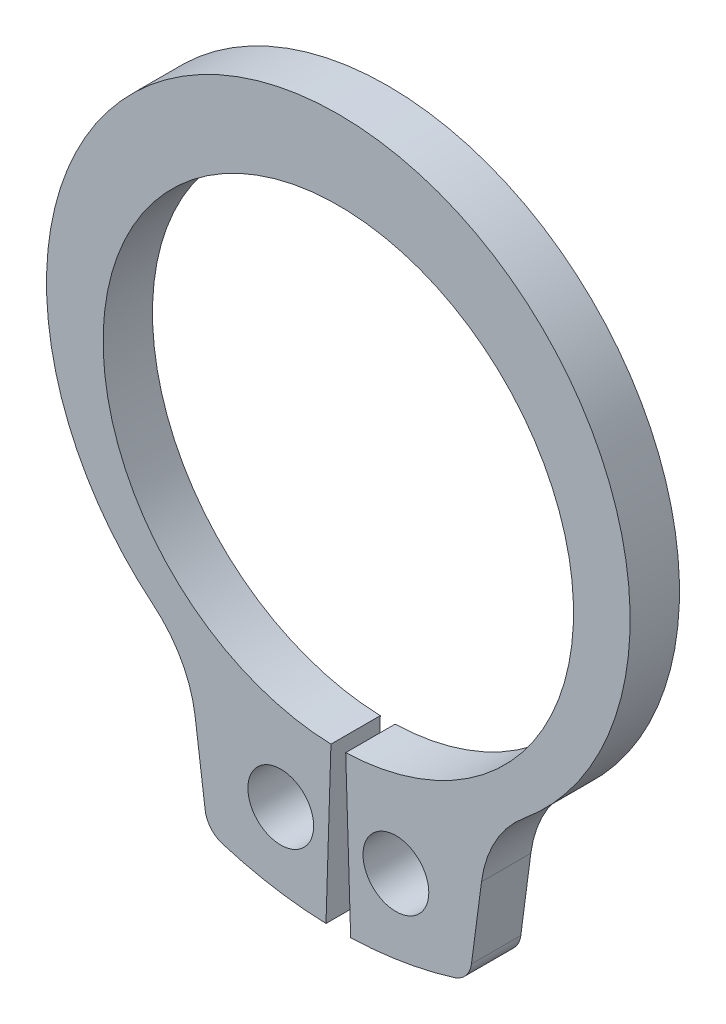
SolidWorks part; units mm, degrees
ref_plane "Plane1" through (0, 0, 0) normal (0, 0, 1) x (1, 0, 0)
ref_plane "Plane2" through (0, 0, 0) normal (0, 1, 0) x (1, 0, 0)
ref_plane "Plane3" through (0, 0, 0) normal (1, 0, 0) x (0, 0, -1)
sketch "Clipboard" plane through (0, 0, 0) normal (0, 0, 1) x (1, 0, 0)
  line L0 (0, 0) -> (2.4, 0)
  line L1 (0, 0) -> (0, 1.2)
  line L2 (0, 0) -> (0, -4.8)
  circle A0 centre (0, 0) radius 1
  circle A1 centre (0, 0) radius 7.5
  dimension "HoleDia" = 2
  dimension "ShaftDia" = 15
  dimension "LargeSection" = 2.4
  dimension "SmallSection" = 1.2
  dimension "LugSection" = 4.8
sketch "BodySke" plane through (0, 0, 0) normal (0, 0, 1) x (1, 0, 0)
  line L0 (-1.5431, 0) -> (1.5431, 0) construction
  line L1 (0, 0) -> (0, 9.55) construction
  line L2 (0.2244, -7.1465) -> (0.375, -11.9441)
  line L3 (-0.2244, -7.1465) -> (-0.375, -11.9441)
  line L4 (0, 0) -> (7.918, -8.9503) construction
  line L5 (0, 0) -> (-7.918, -8.9503) construction
  line L7 (4.3521, -8.4808) -> (4.0468, -10.7997)
  line L8 (-4.3521, -8.4808) -> (-4.0468, -10.7997)
  circle A0 centre (0, 0) radius 7.15 construction
  arc A1 (0.2244, -7.1465) -> (-0.2244, -7.1465) centre (0, 0) ccw
  arc A2 (5.5327, -6.254) -> (-5.5327, -6.254) centre (0, 0.6796) ccw construction
  arc A3 (0.375, -11.9441) -> (3.5244, -11.4185) centre (0, 0) ccw
  arc A4 (5.6337, -6.1721) -> (4.3521, -8.4808) centre (7.918, -8.9503) ccw
  arc A5 (-4.3521, -8.4808) -> (-5.6337, -6.1721) centre (-7.918, -8.9503) ccw
  arc A6 (-3.5244, -11.4185) -> (-0.375, -11.9441) centre (0, 0) ccw
  arc A7 (5.6337, -6.1721) -> (-5.6337, -6.1721) centre (0, 0.6796) ccw
  arc A8 (-4.3216, -8.712) -> (4.3216, -8.712) centre (0, 0) ccw construction
  circle A9 centre (1.75, -9.5662) radius 1
  circle A10 centre (-1.75, -9.5662) radius 1
  arc A11 (4.0468, -10.7997) -> (3.5244, -11.4185) centre (3.3032, -10.7018) cw
  arc A12 (-4.0468, -10.7997) -> (-3.5244, -11.4185) centre (-3.3032, -10.7018) ccw
  point P28 (3.9854, -11.2658)
  point P31 (-3.9854, -11.2658)
  dimension "HoleDia" = 2
  dimension "GrooveDia" = 14.3
  dimension "LugRad" = 11.95
  dimension "HoleOffsetRad" = 9.725
  dimension "D3" = 0.75
  dimension "LargeRad" = 9.55
  dimension "SmallRad" = 8.35
  dimension "SmallAngle" = 82.996
  dimension "D2" = 15
  dimension "HoleSpacing" = 3.5
  dimension "Gap" = 0.75
extrude "Body" add sketch "BodySke" against normal blind 1.5
sketch "NotSke" plane through (0, 0, 0) normal (0, 0, 1) x (1, 0, 0)
  line L0 (1.75, -8.5662) -> (1.75, -10.5662)
  line L1 (1.75, -10.5662) -> (-1.75, -10.5662)
  line L2 (-1.75, -10.5662) -> (-1.75, -8.5662)
  line L3 (-1.75, -8.5662) -> (1.75, -8.5662)
  circle A0 centre (1.75, -9.5662) radius 1 construction
  circle A1 centre (-1.75, -9.5662) radius 1 construction
extrude "Notch" [suppressed] cut sketch "NotSke" against normal through all
sketch "UnlSke" plane through (0, 0, 0) normal (0, 0, 1) x (1, 0, 0)
  line L0 (-3.3477, -11.4715) -> (-2.003, -6.8637)
  line L1 (3.3477, -11.4715) -> (2.003, -6.8637)
  arc A0 (2.003, -6.8637) -> (-2.003, -6.8637) centre (0, 0) ccw
  arc A1 (3.3477, -11.4715) -> (-3.3477, -11.4715) centre (0, 0) ccw
  arc A2 (0.375, -11.9441) -> (3.5244, -11.4185) centre (0, 0) ccw construction
  arc A3 (0.2244, -7.1465) -> (-0.2244, -7.1465) centre (0, 0) ccw construction
  circle A4 centre (-1.75, -9.5662) radius 1 construction
  circle A5 centre (1.75, -9.5662) radius 1 construction
extrude "Unlug" [suppressed] add sketch "UnlSke" against normal through all
equation "' \"ShaftDia@Clipboard\" = 15"
equation "' \"Thickness@Body\" = 1.5"
equation "' \"GrooveDia@BodySke\" = 14.3"
equation "' \"LugSection@Clipboard\" = 4.8"
equation "' \"LargeSection@Clipboard\" = 2.4"
equation "' \"HoleDia@Clipboard\" = 2.0"
equation "' \"ShaftDia@Clipboard\" = 50"
equation "' \"Thickness@Body\" = 3"
equation "' \"GrooveDia@BodySke\" = 47"
equation "' \"LugSection@Clipboard\" = 8"
equation "' \"LargeSection@Clipboard\" = 5.1"
equation "' \"HoleDia@Clipboard\" = 2.5"
equation "\"SmallSection@Clipboard\" = \"LargeSection@Clipboard\" * 0.5"
equation "\"Gap@BodySke\" =  \"Thickness@Body\" / 2"
equation "\"LargeRad@BodySke\" =  \"GrooveDia@BodySke\" / 2 +  \"LargeSection@Clipboard\""
equation "\"SmallRad@BodySke\" =  \"GrooveDia@BodySke\" / 2 +  \"SmallSection@Clipboard\""
equation "\"LugRad@BodySke\" = \"GrooveDia@BodySke\" / 2 + \"LugSection@Clipboard\""
equation "\"HoleOffsetRad@BodySke\" = (  \"ShaftDia@Clipboard\" / 2 + \"LugRad@BodySke\" ) / 2"
equation "\"HoleSpacing@BodySke\" = \"Gap@BodySke\"  * 2 +  \"HoleDia@Clipboard\""
equation "\"HoleDia@BodySke\" =  \"HoleDia@Clipboard\""
equation "\"SmallAngle@BodySke\" = atn(\"HoleSpacing@BodySke\" / 2 / sqr(\"HoleOffsetRad@BodySke\"  * \"HoleOffsetRad@BodySke\" - (\"HoleSpacing@BodySke\" / 2) * (\"HoleSpacing@BodySke\" / 2) ))  * 7 *  (\"LargeRad@BodySke\" / \"SmallRad@BodySke\")* ( 180 / 3.141593)"
